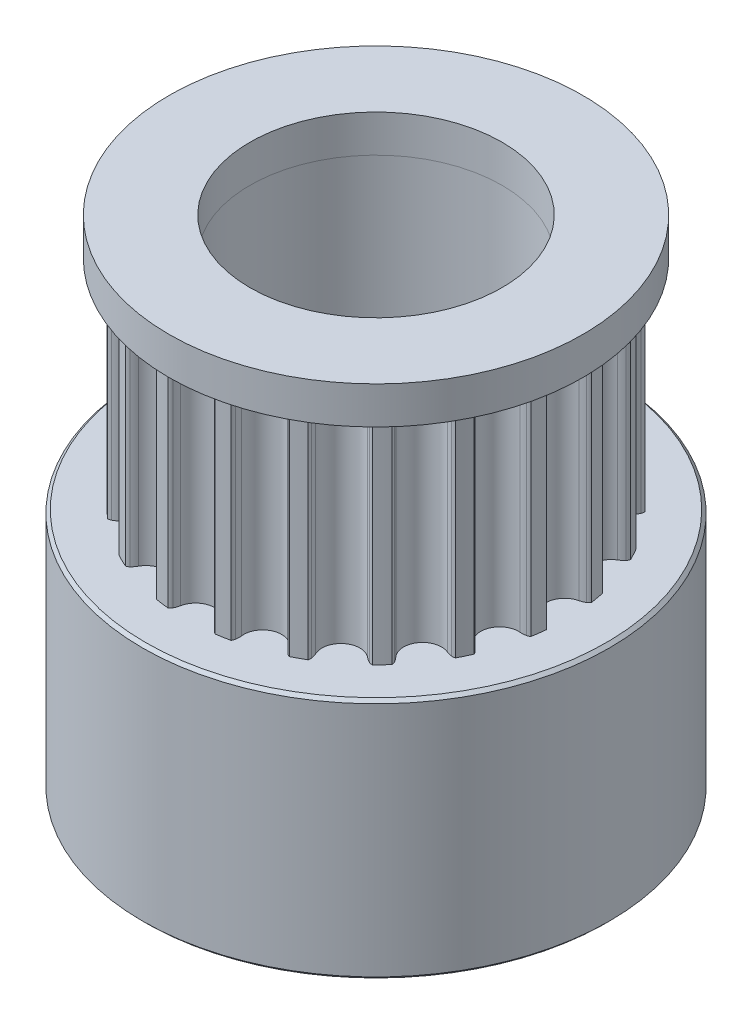
SolidWorks part; units mm, degrees
material "6061 slitina"
ref_plane "Přední rovina" through (0, 0, 0) normal (0, 0, 1) x (1, 0, 0)
ref_plane "Horní rovina" through (0, 0, 0) normal (0, 1, 0) x (1, 0, 0)
ref_plane "Pravá rovina" through (0, 0, 0) normal (1, 0, 0) x (0, 0, -1)
sketch "Skica1" plane through (0, 0, 0) normal (0, 1, 0) x (1, 0, 0)
  circle A0 centre (0, 0) radius 2.5
  arc B0 (-5.7301, 1.0983) -> (-5.3872, 2.2403) centre (-5.6803, 1.7058) ccw
  arc B1 (-5.7301, 1.0983) -> (-5.922, 1.0859) centre (-5.7841, 0.4401) ccw
  arc B2 (-5.922, 1.0859) -> (-6.0197, 1.0387) centre (-5.8743, 0.8624) ccw
  arc B3 (-6.0197, 1.0387) -> (-6.0791, 0.6004) centre (0, 0) ccw
  arc B4 (-6.0791, 0.6004) -> (-5.9974, 0.5289) centre (-5.892, 0.7317) ccw
  arc B5 (-5.9974, 0.5289) -> (-5.8158, 0.466) centre (-5.6927, 1.1148) ccw
  arc B6 (-5.7891, -0.7262) -> (-5.8158, 0.466) centre (-5.9294, -0.133) ccw
  arc B7 (-5.7891, -0.7262) -> (-5.9677, -0.7972) centre (-5.637, -1.3689) ccw
  arc B8 (-5.9677, -0.7972) -> (-6.0461, -0.8723) centre (-5.8532, -0.9951) ccw
  arc B9 (-6.0461, -0.8723) -> (-5.9671, -1.3075) centre (0, 0) ccw
  arc B10 (-5.9671, -1.3075) -> (-5.8673, -1.3503) centre (-5.8297, -1.1248) ccw
  arc B11 (-5.8673, -1.3503) -> (-5.6751, -1.354) centre (-5.7586, -0.6989) ccw
  arc B12 (-5.2813, -2.4796) -> (-5.6751, -1.354) centre (-5.5981, -1.9587) ccw
  arc B13 (-5.2813, -2.4796) -> (-5.4293, -2.6023) centre (-4.9381, -3.0438) ccw
  arc B14 (-5.4293, -2.6023) -> (-5.4806, -2.698) centre (-5.2593, -2.7551) ccw
  arc B15 (-5.4806, -2.698) -> (-5.271, -3.0875) centre (0, 0) ccw
  arc B16 (-5.271, -3.0875) -> (-5.1629, -3.0973) centre (-5.1968, -2.8713) ccw
  arc B17 (-5.1629, -3.0973) -> (-4.979, -3.0415) centre (-5.2608, -2.4442) ccw
  arc B18 (-4.2566, -3.9902) -> (-4.979, -3.0415) centre (-4.7188, -3.5928) ccw
  arc B19 (-4.2566, -3.9902) -> (-4.3594, -4.1527) centre (-3.7559, -4.4208) ccw
  arc B20 (-4.3594, -4.1527) -> (-4.3786, -4.2595) centre (-4.1505, -4.2455) ccw
  arc B21 (-4.3786, -4.2595) -> (-4.059, -4.5652) centre (0, 0) ccw
  arc B22 (-4.059, -4.5652) -> (-3.9531, -4.5412) centre (-4.0552, -4.3366) ccw
  arc B23 (-3.9531, -4.5412) -> (-3.7954, -4.4312) centre (-4.248, -3.9503) ccw
  arc B24 (-2.8152, -5.1103) -> (-3.7954, -4.4312) centre (-3.3776, -4.8751) ccw
  arc B25 (-2.8152, -5.1103) -> (-2.8628, -5.2965) centre (-2.2059, -5.3651) ccw
  arc B26 (-2.8628, -5.2965) -> (-2.8481, -5.4041) centre (-2.6354, -5.3203) ccw
  arc B27 (-2.8481, -5.4041) -> (-2.4496, -5.596) centre (0, 0) ccw
  arc B28 (-2.4496, -5.596) -> (-2.3563, -5.5405) centre (-2.5166, -5.3775) ccw
  arc B29 (-2.3563, -5.5405) -> (-2.2403, -5.3872) centre (-2.8194, -5.0696) ccw
  arc B30 (-1.0983, -5.7301) -> (-2.2403, -5.3872) centre (-1.7058, -5.6803) ccw
  arc B31 (-1.0983, -5.7301) -> (-1.0859, -5.922) centre (-0.4401, -5.7841) ccw
  arc B32 (-1.0859, -5.922) -> (-1.0387, -6.0197) centre (-0.8624, -5.8743) ccw
  arc B33 (-1.0387, -6.0197) -> (-0.6004, -6.0791) centre (0, 0) ccw
  arc B34 (-0.6004, -6.0791) -> (-0.5289, -5.9974) centre (-0.7317, -5.892) ccw
  arc B35 (-0.5289, -5.9974) -> (-0.466, -5.8158) centre (-1.1148, -5.6927) ccw
  arc B36 (0.7262, -5.7891) -> (-0.466, -5.8158) centre (0.133, -5.9294) ccw
  arc B37 (0.7262, -5.7891) -> (0.7972, -5.9677) centre (1.3689, -5.637) ccw
  arc B38 (0.7972, -5.9677) -> (0.8723, -6.0461) centre (0.9951, -5.8532) ccw
  arc B39 (0.8723, -6.0461) -> (1.3075, -5.9671) centre (0, 0) ccw
  arc B40 (1.3075, -5.9671) -> (1.3503, -5.8673) centre (1.1248, -5.8297) ccw
  arc B41 (1.3503, -5.8673) -> (1.354, -5.6751) centre (0.6989, -5.7586) ccw
  arc B42 (2.4796, -5.2813) -> (1.354, -5.6751) centre (1.9587, -5.5981) ccw
  arc B43 (2.4796, -5.2813) -> (2.6023, -5.4293) centre (3.0438, -4.9381) ccw
  arc B44 (2.6023, -5.4293) -> (2.698, -5.4806) centre (2.7551, -5.2593) ccw
  arc B45 (2.698, -5.4806) -> (3.0875, -5.271) centre (0, 0) ccw
  arc B46 (3.0875, -5.271) -> (3.0973, -5.1629) centre (2.8713, -5.1968) ccw
  arc B47 (3.0973, -5.1629) -> (3.0415, -4.979) centre (2.4442, -5.2608) ccw
  arc B48 (3.9902, -4.2566) -> (3.0415, -4.979) centre (3.5928, -4.7188) ccw
  arc B49 (3.9902, -4.2566) -> (4.1527, -4.3594) centre (4.4208, -3.7559) ccw
  arc B50 (4.1527, -4.3594) -> (4.2595, -4.3786) centre (4.2455, -4.1505) ccw
  arc B51 (4.2595, -4.3786) -> (4.5652, -4.059) centre (0, 0) ccw
  arc B52 (4.5652, -4.059) -> (4.5412, -3.9531) centre (4.3366, -4.0552) ccw
  arc B53 (4.5412, -3.9531) -> (4.4312, -3.7954) centre (3.9503, -4.248) ccw
  arc B54 (5.1103, -2.8152) -> (4.4312, -3.7954) centre (4.8751, -3.3776) ccw
  arc B55 (5.1103, -2.8152) -> (5.2965, -2.8628) centre (5.3651, -2.2059) ccw
  arc B56 (5.2965, -2.8628) -> (5.4041, -2.8481) centre (5.3203, -2.6354) ccw
  arc B57 (5.4041, -2.8481) -> (5.596, -2.4496) centre (0, 0) ccw
  arc B58 (5.596, -2.4496) -> (5.5405, -2.3563) centre (5.3775, -2.5166) ccw
  arc B59 (5.5405, -2.3563) -> (5.3872, -2.2403) centre (5.0696, -2.8194) ccw
  arc B60 (5.7301, -1.0983) -> (5.3872, -2.2403) centre (5.6803, -1.7058) ccw
  arc B61 (5.7301, -1.0983) -> (5.922, -1.0859) centre (5.7841, -0.4401) ccw
  arc B62 (5.922, -1.0859) -> (6.0197, -1.0387) centre (5.8743, -0.8624) ccw
  arc B63 (6.0197, -1.0387) -> (6.0791, -0.6004) centre (0, 0) ccw
  arc B64 (6.0791, -0.6004) -> (5.9974, -0.5289) centre (5.892, -0.7317) ccw
  arc B65 (5.9974, -0.5289) -> (5.8158, -0.466) centre (5.6927, -1.1148) ccw
  arc B66 (5.7891, 0.7262) -> (5.8158, -0.466) centre (5.9294, 0.133) ccw
  arc B67 (5.7891, 0.7262) -> (5.9677, 0.7972) centre (5.637, 1.3689) ccw
  arc B68 (5.9677, 0.7972) -> (6.0461, 0.8723) centre (5.8532, 0.9951) ccw
  arc B69 (6.0461, 0.8723) -> (5.9671, 1.3075) centre (0, 0) ccw
  arc B70 (5.9671, 1.3075) -> (5.8673, 1.3503) centre (5.8297, 1.1248) ccw
  arc B71 (5.8673, 1.3503) -> (5.6751, 1.354) centre (5.7586, 0.6989) ccw
  arc B72 (5.2813, 2.4796) -> (5.6751, 1.354) centre (5.5981, 1.9587) ccw
  arc B73 (5.2813, 2.4796) -> (5.4293, 2.6023) centre (4.9381, 3.0438) ccw
  arc B74 (5.4293, 2.6023) -> (5.4806, 2.698) centre (5.2593, 2.7551) ccw
  arc B75 (5.4806, 2.698) -> (5.271, 3.0875) centre (0, 0) ccw
  arc B76 (5.271, 3.0875) -> (5.1629, 3.0973) centre (5.1968, 2.8713) ccw
  arc B77 (5.1629, 3.0973) -> (4.979, 3.0415) centre (5.2608, 2.4442) ccw
  arc B78 (4.2566, 3.9902) -> (4.979, 3.0415) centre (4.7188, 3.5928) ccw
  arc B79 (4.2566, 3.9902) -> (4.3594, 4.1527) centre (3.7559, 4.4208) ccw
  arc B80 (4.3594, 4.1527) -> (4.3786, 4.2595) centre (4.1505, 4.2455) ccw
  arc B81 (4.3786, 4.2595) -> (4.059, 4.5652) centre (0, 0) ccw
  arc B82 (4.059, 4.5652) -> (3.9531, 4.5412) centre (4.0552, 4.3366) ccw
  arc B83 (3.9531, 4.5412) -> (3.7954, 4.4312) centre (4.248, 3.9503) ccw
  arc B84 (2.8152, 5.1103) -> (3.7954, 4.4312) centre (3.3776, 4.8751) ccw
  arc B85 (2.8152, 5.1103) -> (2.8628, 5.2965) centre (2.2059, 5.3651) ccw
  arc B86 (2.8628, 5.2965) -> (2.8481, 5.4041) centre (2.6354, 5.3203) ccw
  arc B87 (2.8481, 5.4041) -> (2.4496, 5.596) centre (0, 0) ccw
  arc B88 (2.4496, 5.596) -> (2.3563, 5.5405) centre (2.5166, 5.3775) ccw
  arc B89 (2.3563, 5.5405) -> (2.2403, 5.3872) centre (2.8194, 5.0696) ccw
  arc B90 (1.0983, 5.7301) -> (2.2403, 5.3872) centre (1.7058, 5.6803) ccw
  arc B91 (1.0983, 5.7301) -> (1.0859, 5.922) centre (0.4401, 5.7841) ccw
  arc B92 (1.0859, 5.922) -> (1.0387, 6.0197) centre (0.8624, 5.8743) ccw
  arc B93 (1.0387, 6.0197) -> (0.6004, 6.0791) centre (0, 0) ccw
  arc B94 (0.6004, 6.0791) -> (0.5289, 5.9974) centre (0.7317, 5.892) ccw
  arc B95 (0.5289, 5.9974) -> (0.466, 5.8158) centre (1.1148, 5.6927) ccw
  arc B96 (-0.7262, 5.7891) -> (0.466, 5.8158) centre (-0.133, 5.9294) ccw
  arc B97 (-0.7262, 5.7891) -> (-0.7972, 5.9677) centre (-1.3689, 5.637) ccw
  arc B98 (-0.7972, 5.9677) -> (-0.8723, 6.0461) centre (-0.9951, 5.8532) ccw
  arc B99 (-0.8723, 6.0461) -> (-1.3075, 5.9671) centre (0, 0) ccw
  arc B100 (-1.3075, 5.9671) -> (-1.3503, 5.8673) centre (-1.1248, 5.8297) ccw
  arc B101 (-1.3503, 5.8673) -> (-1.354, 5.6751) centre (-0.6989, 5.7586) ccw
  arc B102 (-2.4796, 5.2813) -> (-1.354, 5.6751) centre (-1.9587, 5.5981) ccw
  arc B103 (-2.4796, 5.2813) -> (-2.6023, 5.4293) centre (-3.0438, 4.9381) ccw
  arc B104 (-2.6023, 5.4293) -> (-2.698, 5.4806) centre (-2.7551, 5.2593) ccw
  arc B105 (-2.698, 5.4806) -> (-3.0875, 5.271) centre (0, 0) ccw
  arc B106 (-3.0875, 5.271) -> (-3.0973, 5.1629) centre (-2.8713, 5.1968) ccw
  arc B107 (-3.0973, 5.1629) -> (-3.0415, 4.979) centre (-2.4442, 5.2608) ccw
  arc B108 (-3.9902, 4.2566) -> (-3.0415, 4.979) centre (-3.5928, 4.7188) ccw
  arc B109 (-3.9902, 4.2566) -> (-4.1527, 4.3594) centre (-4.4208, 3.7559) ccw
  arc B110 (-4.1527, 4.3594) -> (-4.2595, 4.3786) centre (-4.2455, 4.1505) ccw
  arc B111 (-4.2595, 4.3786) -> (-4.5652, 4.059) centre (0, 0) ccw
  arc B112 (-4.5652, 4.059) -> (-4.5412, 3.9531) centre (-4.3366, 4.0552) ccw
  arc B113 (-4.5412, 3.9531) -> (-4.4312, 3.7954) centre (-3.9503, 4.248) ccw
  arc B114 (-5.1103, 2.8152) -> (-4.4312, 3.7954) centre (-4.8751, 3.3776) ccw
  arc B115 (-5.1103, 2.8152) -> (-5.2965, 2.8628) centre (-5.3651, 2.2059) ccw
  arc B116 (-5.2965, 2.8628) -> (-5.4041, 2.8481) centre (-5.3203, 2.6354) ccw
  arc B117 (-5.4041, 2.8481) -> (-5.596, 2.4496) centre (0, 0) ccw
  arc B118 (-5.596, 2.4496) -> (-5.5405, 2.3563) centre (-5.3775, 2.5166) ccw
  arc B119 (-5.5405, 2.3563) -> (-5.3872, 2.2403) centre (-5.0696, 2.8194) ccw
  dimension "D1" = 5
sketch_block_instance "Blok1-1"
sketch_block "Blok1"
extrude "Přidat vysunutím1" add sketch "Skica1" along normal blind 7 from offset 7.8
sketch "Skica2" plane through (0, 7.8, 0) normal (0, -1, 0) x (1, 0, 0)
  circle A0 centre (0, 0) radius 3.5
  circle A1 centre (0, 0) radius 2.5 construction
  circle A2 centre (0, 0) radius 2.5
  dimension "D1" = 7
extrude "Přidat vysunutím2" add sketch "Skica2" along normal blind 7.8
sketch "Skica3" plane through (0, 14.8, 0) normal (0, 1, 0) x (1, 0, 0)
  circle A0 centre (0, 0) radius 3.5
  circle A1 centre (0, 0) radius 2.5 construction
  circle A2 centre (0, 0) radius 2.5
  dimension "D1" = 7
extrude "Přidat vysunutím3" add sketch "Skica3" along normal blind 1.2
sketch "Skica5" plane through (0, 16, 0) normal (0, 1, 0) x (1, 0, 0)
  circle A0 centre (0, 0) radius 7.5
  circle A3 centre (0, 0) radius 3.5 construction
  circle A4 centre (0, 0) radius 3.5
  dimension "D1" = 15
extrude "Přidat vysunutím4" add sketch "Skica5" against normal up to surface (1.2 mm away) separate body up to face at (0, 14.8, 0)
sketch "Skica6" plane through (0, 0, 0) normal (0, -1, 0) x (1, 0, 0)
  circle A0 centre (0, 0) radius 7.5
  circle A1 centre (0, 0) radius 3.5 construction
  circle A2 centre (0, 0) radius 3.5
  circle A3 centre (0, 0) radius 7.5 construction
extrude "Přidat vysunutím5" add sketch "Skica6" against normal up to surface (7.8 mm away) separate body up to face at (0, 7.8, 0)
chamfer "Zkosení1" distance 0.1 angle 45 2 edges at (0, 14.8, 7.5) (0, 16, 7.5)
chamfer "Zkosení2" distance 0.1 angle 45 2 edges at (0, 0, -2.5) (0, 16, 2.5)
chamfer "Zkosení3" distance 0.1 angle 45 2 edges at (0, 0, -7.5) (0, 7.8, 7.5)
sketch "Sketch7" plane through (0, 0, 0) normal (0, -1, 0) x (1, 0, 0)
  circle A1 centre (0, 0) radius 4.05
  dimension "D1" = 8.1
sketch "Sketch8" plane through (0, 16, 0) normal (0, 1, 0) x (1, 0, 0)
  circle A0 centre (0, 0) radius 6.65
extrude "Cut-Extrude2" cut sketch "Sketch8" against normal blind 5 flip side to cut contours A0
ref_plane "Plane1" through (0, 0, -7.5) normal (0, 0, -1) x (-1, 0, 0)
ref_plane "Plane2" through (-7.5, 0, 0) normal (-1, 0, 0) x (0, 0, 1)
sketch "Sketch19" plane through (0, 0, -7.5) normal (0, 0, -1) x (-1, 0, 0)
  line L0 (0, 0.1) -> (0, 7.7)
  line L1 (7.5, 0.1) -> (-7.5, 0.1) construction
  line L2 (7.5, 7.7) -> (-7.5, 7.7) construction
  circle A0 centre (0, 3.9) radius 1.5
extrude "Cut-Extrude6" cut sketch "Sketch19" against normal blind 5 contours A0
sketch "Sketch20" plane through (-7.5, 0, 0) normal (-1, 0, 0) x (0, 0, 1)
  line L0 (0, 0.1) -> (0, 7.7)
  line L1 (-7.5, 0.1) -> (7.5, 0.1) construction
  line L2 (7.5, 7.7) -> (-7.5, 7.7) construction
  circle A0 centre (0, 3.9) radius 1.5
extrude "Cut-Extrude7" cut sketch "Sketch20" against normal blind 5 contours A0
extrude "Cut-Extrude9" cut sketch "Sketch7" against normal blind 20 contours A1
